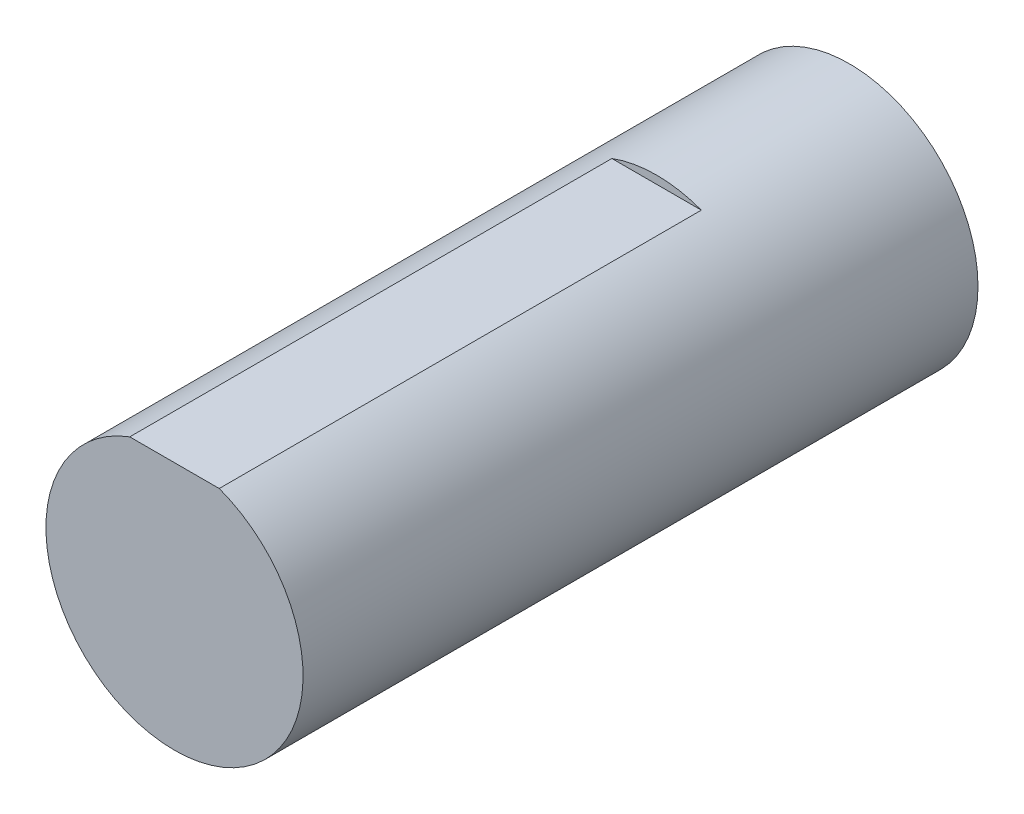
SolidWorks part; units mm, degrees
ref_plane "Front Plane" through (0, 0, 0) normal (0, 0, 1) x (1, 0, 0)
ref_plane "Top Plane" through (0, 0, 0) normal (0, 1, 0) x (1, 0, 0)
ref_plane "Right Plane" through (0, 0, 0) normal (1, 0, 0) x (0, 0, -1)
sketch "Sketch1" plane through (0, 0, 0) normal (0, 0, 1) x (1, 0, 0)
  circle A0 centre (0, 0) radius 4
  dimension "D1" = 8
extrude "Boss-Extrude1" add sketch "Sketch1" along normal blind 21
sketch "Sketch2" plane through (0, 0, 21) normal (0, 0, 1) x (1, 0, 0)
  line L0 (-1.3919, 3.75) -> (1.3919, 3.75)
  circle A0 centre (0, 0) radius 4 construction
  dimension "D1" = 3.75
extrude "Cut-Extrude1" cut sketch "Sketch2" against normal blind 15 and the other way through all
